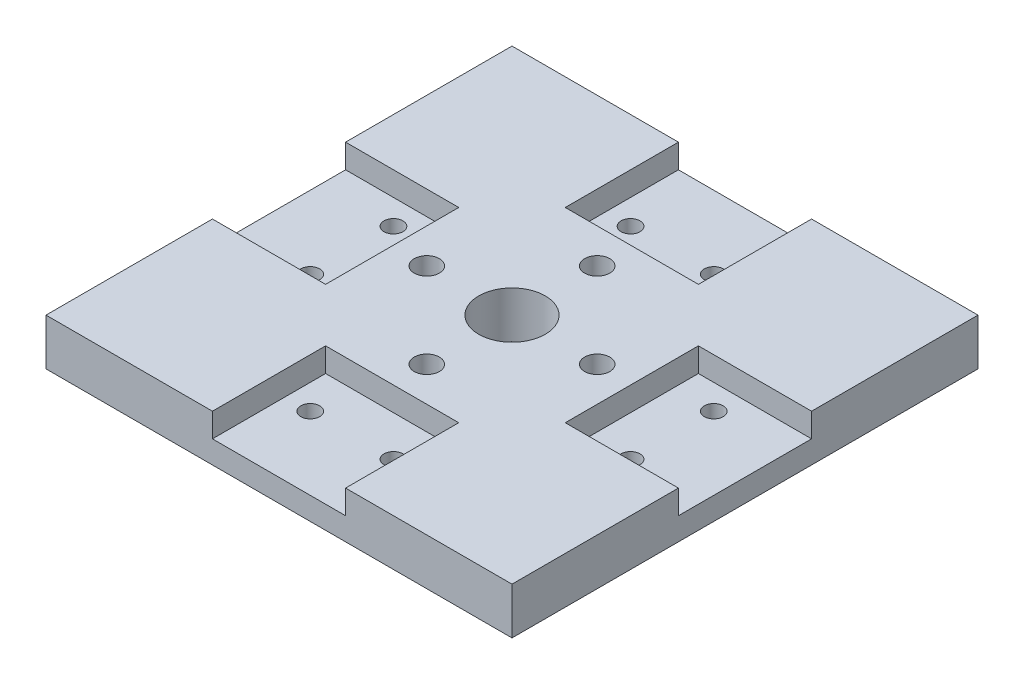
SolidWorks part; units mm, degrees
material "6061 Alloy"
ref_plane "Front Plane" through (0, 0, 0) normal (0, 0, 1) x (1, 0, 0)
ref_plane "Top Plane" through (0, 0, 0) normal (0, 1, 0) x (1, 0, 0)
ref_plane "Right Plane" through (0, 0, 0) normal (1, 0, 0) x (0, 0, -1)
sketch "Sketch1" plane through (0, 0, 0) normal (0, 1, 0) x (1, 0, 0)
  line L1 (0, 0) -> (88.9, 0)
  line L2 (0, 0) -> (0, 88.9)
  line L3 (0, 88.9) -> (88.9, 88.9)
  line L4 (88.9, 0) -> (88.9, 88.9)
  dimension "D1" = 88.9
  dimension "D2" = 88.9
extrude "Boss-Extrude1" add sketch "Sketch1" along normal blind 8.89
sketch "Sketch2" plane through (0, 8.89, 0) normal (0, 1, 0) x (1, 0, 0)
  line L0 (88.9, 88.9) -> (0, 88.9) construction
  line L1 (31.75, 88.9) -> (57.15, 88.9)
  line L2 (31.75, 88.9) -> (31.75, 67.31)
  line L3 (31.75, 67.31) -> (57.15, 67.31)
  line L4 (57.15, 88.9) -> (57.15, 67.31)
  line L5 (0, 88.9) -> (0, 0) construction
  line L6 (0, 57.15) -> (21.59, 57.15)
  line L7 (0, 57.15) -> (0, 31.75)
  line L8 (0, 31.75) -> (21.59, 31.75)
  line L9 (21.59, 57.15) -> (21.59, 31.75)
  line L10 (0, 0) -> (88.9, 0) construction
  line L11 (31.75, 0) -> (57.15, 0)
  line L12 (31.75, 0) -> (31.75, 21.59)
  line L13 (31.75, 21.59) -> (57.15, 21.59)
  line L14 (57.15, 0) -> (57.15, 21.59)
  line L15 (88.9, 0) -> (88.9, 88.9) construction
  line L16 (88.9, 57.15) -> (67.31, 57.15)
  line L17 (88.9, 57.15) -> (88.9, 31.75)
  line L18 (88.9, 31.75) -> (67.31, 31.75)
  line L19 (67.31, 57.15) -> (67.31, 31.75)
  dimension "D1" = 31.75
  dimension "D2" = 25.4
  dimension "D3" = 25.4
  dimension "D4" = 31.75
  dimension "D5" = 25.4
  dimension "D6" = 31.75
  dimension "D7" = 25.4
  dimension "D8" = 31.75
  dimension "D9" = 21.59
  dimension "D10" = 21.59
  dimension "D11" = 21.59
  dimension "D12" = 21.59
extrude "Cut-Extrude1" cut sketch "Sketch2" against normal blind 4.572
sketch "Sketch3" plane through (0, 8.89, 0) normal (0, 1, 0) x (1, 0, 0)
  line L0 (31.75, 88.9) -> (0, 88.9) construction
  line L1 (20.6375, 68.2625) -> (68.2625, 68.2625)
  line L2 (20.6375, 68.2625) -> (20.6375, 20.6375)
  line L3 (20.6375, 20.6375) -> (68.2625, 20.6375)
  line L4 (68.2625, 68.2625) -> (68.2625, 20.6375)
  line L5 (88.9, 31.75) -> (88.9, 57.15) construction
  line L6 (0, 57.15) -> (0, 31.75) construction
  line L7 (57.15, 0) -> (88.9, 0) construction
  circle A0 centre (28.194, 44.45) radius 2.4
  circle A1 centre (44.45, 60.706) radius 2.4
  circle A2 centre (60.706, 44.45) radius 2.4
  circle A3 centre (44.45, 28.194) radius 2.4
  dimension "D5" = 4.8
  dimension "D6" = 4.8
  dimension "D7" = 4.8
  dimension "D8" = 4.8
  dimension "D2" = 20.6375
  dimension "D3" = 20.6375
  dimension "D4" = 47.625
  dimension "D9" = 28.194
  dimension "D10" = 28.194
  dimension "D11" = 28.194
  dimension "D12" = 28.194
  dimension "D13" = 23.8125
  dimension "D14" = 23.8125
  dimension "D15" = 23.8125
  dimension "D16" = 23.8125
extrude "Cut-Extrude2" cut sketch "Sketch3" against normal through all contours A2 | A1 | A0 | A3
sketch "Sketch4" plane through (0, 4.318, 0) normal (0, 1, 0) x (1, 0, 0)
  line L0 (0, 57.15) -> (0, 31.75) construction
  line L1 (57.15, 88.9) -> (31.75, 88.9) construction
  line L2 (88.9, 31.75) -> (88.9, 57.15) construction
  line L3 (31.75, 0) -> (57.15, 0) construction
  line L4 (0, 31.75) -> (21.59, 31.75) construction
  line L5 (31.75, 21.59) -> (31.75, 0) construction
  line L6 (67.31, 31.75) -> (88.9, 31.75) construction
  line L7 (57.15, 67.31) -> (57.15, 88.9) construction
  circle A0 centre (75.0062, 52.3875) radius 1.8034
  circle A1 centre (75.0062, 36.5125) radius 1.8034
  circle A2 centre (52.3875, 75.0062) radius 1.8034
  circle A3 centre (36.5125, 75.0062) radius 1.8034
  circle A4 centre (13.8938, 52.3875) radius 1.8034
  circle A5 centre (13.8938, 36.5125) radius 1.8034
  circle A6 centre (36.5125, 13.8938) radius 1.8034
  circle A7 centre (52.3875, 13.8938) radius 1.8034
  dimension "D1" = 3.6068
  dimension "D2" = 3.6068
  dimension "D3" = 3.6068
  dimension "D4" = 3.6068
  dimension "D5" = 3.6068
  dimension "D6" = 3.6068
  dimension "D7" = 3.6068
  dimension "D8" = 3.6068
  dimension "D9" = 13.8938
  dimension "D10" = 13.8938
  dimension "D11" = 13.8938
  dimension "D12" = 13.8938
  dimension "D13" = 13.8938
  dimension "D14" = 13.8938
  dimension "D15" = 13.8938
  dimension "D16" = 13.8938
  dimension "D17" = 15.875
  dimension "D18" = 4.7625
  dimension "D19" = 4.7625
  dimension "D20" = 15.875
  dimension "D21" = 4.7625
  dimension "D22" = 15.875
  dimension "D23" = 4.7625
  dimension "D24" = 15.875
extrude "Cut-Extrude3" cut sketch "Sketch4" against normal through all
sketch "Sketch5" plane through (0, 8.89, 0) normal (0, 1, 0) x (1, 0, 0)
  line L0 (88.9, 88.9) -> (57.15, 88.9) construction
  line L1 (88.9, 31.75) -> (88.9, 57.15) construction
  circle A0 centre (44.45, 44.45) radius 6.35
  dimension "D1" = 12.7
  dimension "D2" = 44.45
  dimension "D3" = 44.45
extrude "Cut-Extrude4" cut sketch "Sketch5" against normal through all
equation "\"hinge_hole\"= 0.142in"
equation "\"D1@Sketch4\"=\"hinge_hole\""
equation "\"D2@Sketch4\"=\"hinge_hole\""
equation "\"D3@Sketch4\"=\"hinge_hole\""
equation "\"D4@Sketch4\"=\"hinge_hole\""
equation "\"D5@Sketch4\"=\"hinge_hole\""
equation "\"D6@Sketch4\"=\"hinge_hole\""
equation "\"D7@Sketch4\"=\"hinge_hole\""
equation "\"D8@Sketch4\"=\"hinge_hole\""
equation "\"hinge_hole_dist\"= 0.297 + 0.25"
equation "\"D9@Sketch4\"=\"hinge_hole_dist\""
equation "\"D10@Sketch4\"=\"hinge_hole_dist\""
equation "\"D11@Sketch4\"=\"hinge_hole_dist\""
equation "\"D12@Sketch4\"=\"hinge_hole_dist\""
equation "\"D13@Sketch4\"=\"hinge_hole_dist\""
equation "\"D14@Sketch4\"=\"hinge_hole_dist\""
equation "\"D15@Sketch4\"=\"hinge_hole_dist\""
equation "\"D16@Sketch4\"=\"hinge_hole_dist\""
equation "\"hinge_hole_sep\"= 0.625"
equation "\"hinge_hole_from_wall\"= ( 1 - \"hinge_hole_sep\" ) / 2"
equation "\"D17@Sketch4\"=\"hinge_hole_sep\""
equation "\"D18@Sketch4\"=\"hinge_hole_from_wall\""
equation "\"D19@Sketch4\"=\"hinge_hole_from_wall\""
equation "\"D20@Sketch4\"=\"hinge_hole_sep\""
equation "\"D21@Sketch4\"=\"hinge_hole_from_wall\""
equation "\"D22@Sketch4\"=\"hinge_hole_sep\""
equation "\"D23@Sketch4\"=\"hinge_hole_from_wall\""
equation "\"D24@Sketch4\"=\"hinge_hole_sep\""
equation "\"D9@Sketch2\"=\"hinge_hole_dist\" + (0.6-0.297)"
equation "\"D12@Sketch2\"=\"hinge_hole_dist\" + (0.6-0.297)"
equation "\"D11@Sketch2\"=\"hinge_hole_dist\" + (0.6-0.297)"
equation "\"D10@Sketch2\"=\"hinge_hole_dist\" + (0.6-0.297)"
